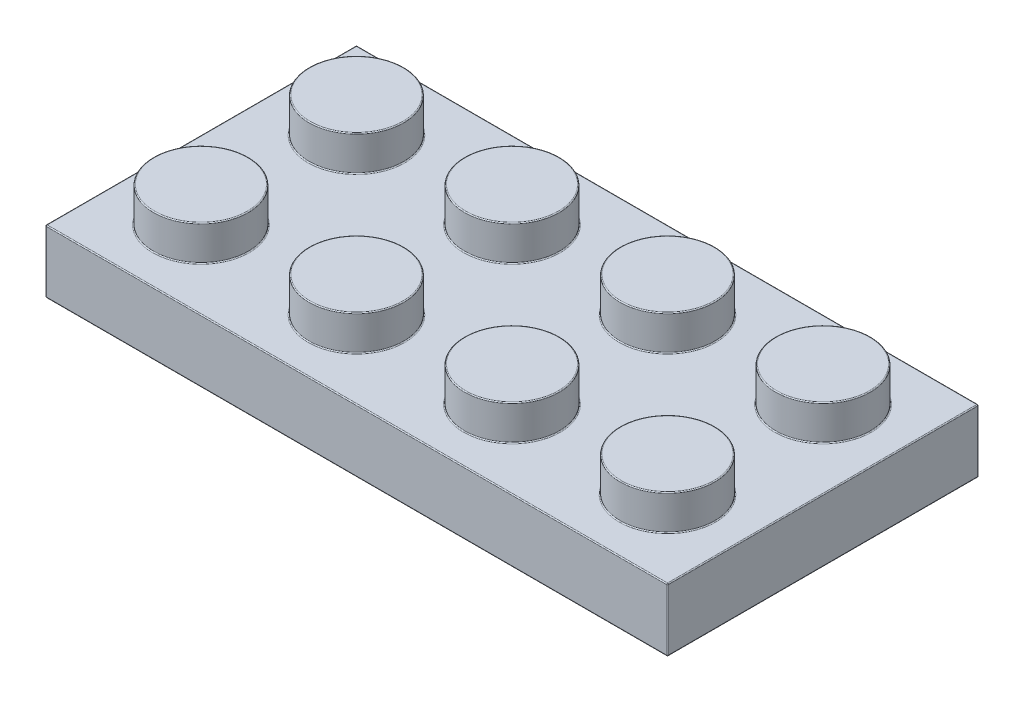
SolidWorks part; units mm, degrees
ref_plane "Front Plane" through (0, 0, 0) normal (0, 0, 1) x (1, 0, 0)
ref_plane "Top Plane" through (0, 0, 0) normal (0, 1, 0) x (1, 0, 0)
ref_plane "Right Plane" through (0, 0, 0) normal (1, 0, 0) x (0, 0, -1)
sketch "Sketch1" plane through (0, 0, 0) normal (0, 1, 0) x (1, 0, 0)
  line L1 (-3.98, 3.98) -> (3.98, 3.98)
  line L2 (-3.98, 3.98) -> (-3.98, -3.98)
  line L3 (-3.98, -3.98) -> (3.98, -3.98)
  line L4 (3.98, 3.98) -> (3.98, -3.98)
  line L5 (-3.98, 3.98) -> (3.98, -3.98) construction
  line L6 (-3.98, -3.98) -> (3.98, 3.98) construction
  point P0 (0, 0)
  dimension "D1" = 7.96
extrude "Extrude1" add sketch "Sketch1" along normal blind 3.22
sketch "Sketch2" plane through (0, 3.22, 0) normal (0, 1, 0) x (1, 0, 0)
  circle A0 centre (0, 0) radius 2.425
  dimension "D1" = 4.85
extrude "Extrude2" add sketch "Sketch2" along normal blind 1.8
pattern_linear "LPattern1" count 4 spacing 7.96 along (1, 0, 0) of "Extrude2", "Extrude1"
pattern_linear "LPattern2" count 2 spacing 7.96 along (0, 0, -1) of "LPattern1", "Extrude1", "Extrude2"
shell "Shell1" thickness 1.55
sketch "Sketch3" plane through (0, 1.67, 0) normal (0, -1, 0) x (1, 0, 0)
  line L0 (26.31, 2.43) -> (26.31, -10.39) construction
  line L1 (-2.43, 2.43) -> (26.31, 2.43) construction
  line L2 (-2.43, -10.39) -> (-2.43, 2.43) construction
  line L3 (26.31, -10.39) -> (-2.43, -10.39) construction
  line L4 (26.31, 2.43) -> (26.31, -10.39)
  line L5 (-2.43, 2.43) -> (26.31, 2.43)
  line L6 (-2.43, -10.39) -> (-2.43, 2.43)
  line L7 (26.31, -10.39) -> (-2.43, -10.39)
extrude "Extrude3" cut sketch "Sketch3" against normal blind 0.14
sketch "Sketch4" plane through (0, 1.81, 0) normal (0, -1, 0) x (1, 0, 0)
  line L0 (3.98, -3.98) -> (11.94, -3.98) construction
  line L1 (0, 0) -> (7.96, 0) construction
  line L2 (0, 0) -> (0, -7.96) construction
  line L3 (0, -7.96) -> (7.96, -7.96) construction
  line L4 (7.96, 0) -> (7.96, -7.96) construction
  line L5 (7.96, 0) -> (15.92, 0) construction
  line L6 (7.96, 0) -> (7.96, -7.96) construction
  line L7 (7.96, -7.96) -> (15.92, -7.96) construction
  line L8 (15.92, 0) -> (15.92, -7.96) construction
  line L9 (15.92, 0) -> (23.88, 0) construction
  line L10 (15.92, 0) -> (15.92, -7.96) construction
  line L11 (15.92, -7.96) -> (23.88, -7.96) construction
  line L12 (23.88, 0) -> (23.88, -7.96) construction
  circle A0 centre (3.98, -3.98) radius 3.23
  circle A1 centre (3.98, -3.98) radius 2.37
  circle A2 centre (11.94, -3.98) radius 2.37
  circle A3 centre (11.94, -3.98) radius 3.23
  circle A4 centre (19.9, -3.98) radius 2.37
  circle A5 centre (19.9, -3.98) radius 3.23
  point P15 (0, -3.98)
  point P16 (3.98, 0)
  point P17 (11.94, 0)
  dimension "D1" = 0.86
  dimension "D2" = 6.46
  dimension "D3" = 7.96
extrude "Extrude4" add sketch "Sketch4" along normal up to surface (1.81 mm away) up to face at (11.94, 0, -3.98)
fillet "Fillet1" radius 0.05 68 edges at (-3.98, 3.22, -3.98) (3.98, 1.81, -0.75) (3.98, 1.81, -6.35) (3.98, 0, -0.75) (3.98, 0, -1.61) (11.94, 3.22, 3.98) (11.94, 1.81, -0.75) (11.94, 1.81, -6.35) (11.94, 0, -0.75) (11.94, 0, -1.61) (19.9, 1.81, -0.75) (0, 3.22, 2.425) (19.9, 1.81, -6.35) (19.9, 0, -0.75) (19.9, 0, -1.61) (0, 5.02, 2.425) (27.86, 3.22, -3.98) (27.86, 0, -3.98) (27.86, 1.61, 3.98) (7.96, 3.22, 2.425) (7.96, 5.02, 2.425) (15.92, 3.22, 2.425) (15.92, 5.02, 2.425) (23.88, 3.22, 2.425) (23.88, 5.02, 2.425) (11.94, 0, -11.94) (27.86, 1.61, -11.94) (-3.98, 1.61, -11.94) (11.94, 3.22, -11.94) (11.94, 0, 3.98) (-3.98, 0, -3.98) (0, 3.22, -5.535) (0, 5.02, -5.535) (7.96, 3.22, -5.535) (7.96, 5.02, -5.535) (15.92, 3.22, -5.535) (15.92, 5.02, -5.535) (23.88, 3.22, -5.535) (23.88, 5.02, -5.535) (-2.43, 0, -3.98) (-2.43, 0.905, -10.39) (11.94, 0, 2.43) (-2.43, 0.905, 2.43) (0, 3.47, 0.875) (26.31, 0, -3.98) (26.31, 0.905, 2.43) (7.96, 3.47, 0.875) (15.92, 3.47, 0.875) (23.88, 3.47, 0.875) (11.94, 0, -10.39) (26.31, 0.905, -10.39) (0, 3.47, -7.085) (7.96, 3.47, -7.085) (15.92, 3.47, -7.085) (23.88, 3.47, -7.085) (-3.98, 1.61, 3.98) (0, 1.81, 0.875) (7.96, 1.81, 0.875) (15.92, 1.81, 0.875) (23.88, 1.81, 0.875) (0, 1.81, -7.085) (7.96, 1.81, -7.085) (15.92, 1.81, -7.085) (23.88, 1.81, -7.085) (11.94, 1.81, 2.43) (26.31, 1.81, -3.98) (11.94, 1.81, -10.39) (-2.43, 1.81, -3.98)
